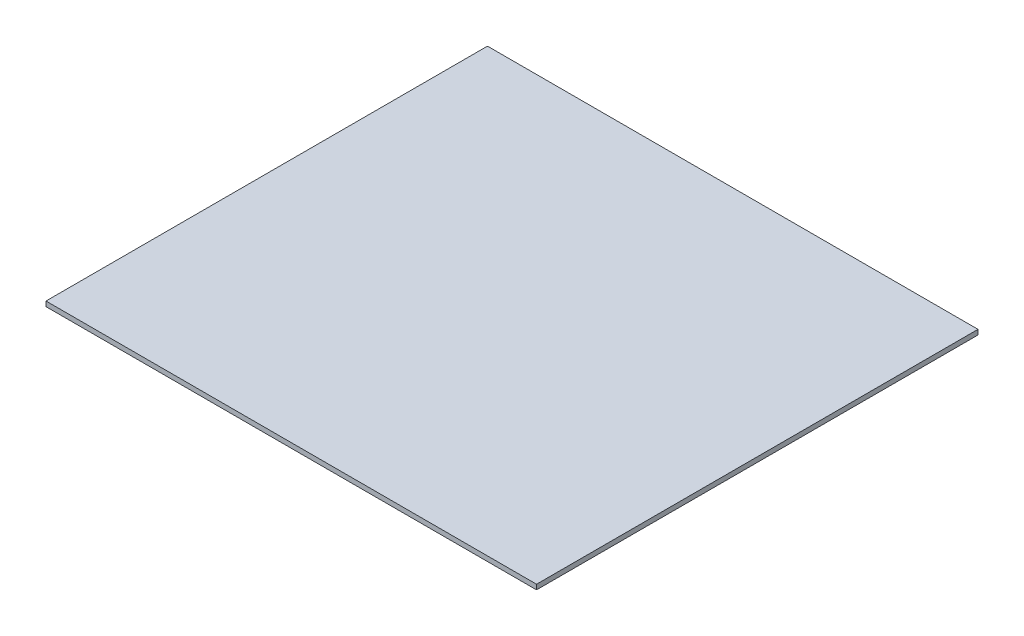
SolidWorks part; units mm, degrees
ref_plane "Front Plane" through (0, 0, 0) normal (0, 0, 1) x (1, 0, 0)
ref_plane "Top Plane" through (0, 0, 0) normal (0, 1, 0) x (1, 0, 0)
ref_plane "Right Plane" through (0, 0, 0) normal (1, 0, 0) x (0, 0, -1)
sketch "Sketch1" plane through (0, 0, 0) normal (0, 1, 0) x (1, 0, 0)
  line L1 (-500, 450) -> (500, 450)
  line L2 (-500, 450) -> (-500, -450)
  line L3 (-500, -450) -> (500, -450)
  line L4 (500, 450) -> (500, -450)
  line L5 (-500, 450) -> (500, -450) construction
  line L6 (-500, -450) -> (500, 450) construction
  point P0 (0, 0)
  dimension "D1" = 1000
  dimension "D2" = 900
extrude "Boss-Extrude1" add sketch "Sketch1" along normal blind 10
